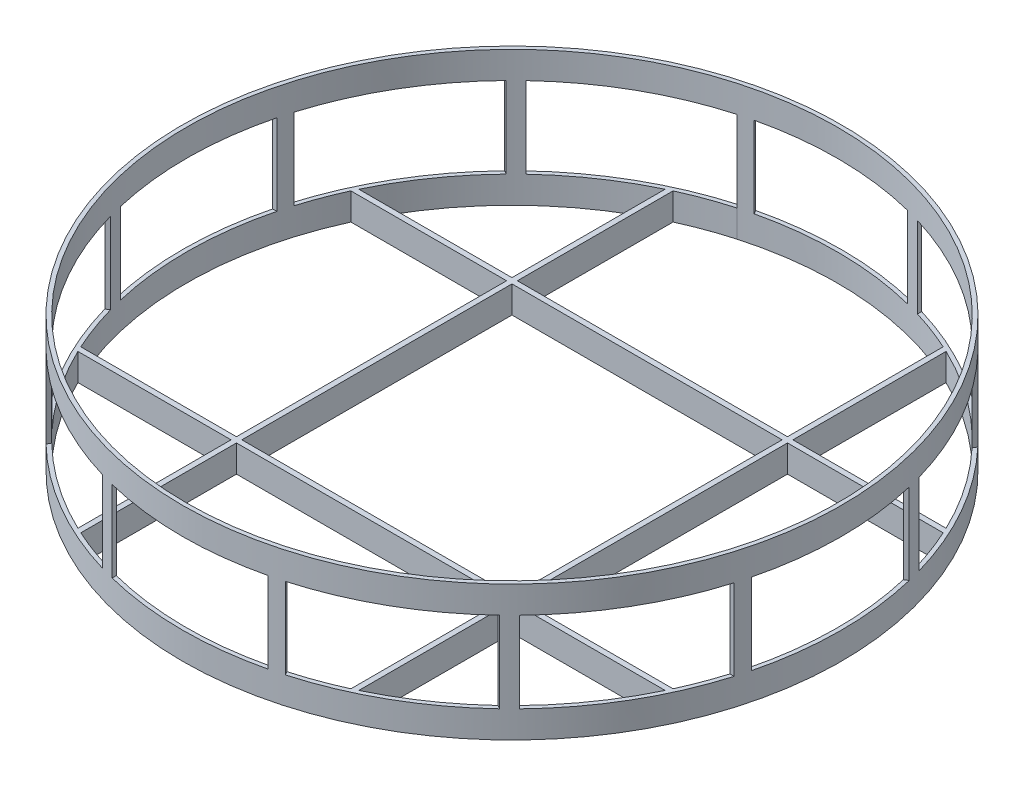
SolidWorks part; units mm, degrees
ref_plane "Front Plane" through (0, 0, 0) normal (0, 0, 1) x (1, 0, 0)
ref_plane "Top Plane" through (0, 0, 0) normal (0, 1, 0) x (1, 0, 0)
ref_plane "Right Plane" through (0, 0, 0) normal (1, 0, 0) x (0, 0, -1)
sketch "Sketch1" plane through (0, 0, 0) normal (0, 1, 0) x (1, 0, 0)
  circle A0 centre (0, 0) radius 120.5
  circle A1 centre (0, 0) radius 122
  dimension "D1" = 241
  dimension "D2" = 244
extrude "Boss-Extrude1" add sketch "Sketch1" along normal blind 10
sketch "Sketch3" plane through (0, 10, 0) normal (0, 1, 0) x (1, 0, 0)
  line L0 (34.7178, 116.9559) -> (34.7178, 115.3903)
  line L1 (29.7178, 118.3252) -> (29.7178, 116.778)
  circle A0 centre (0, 0) radius 122
  circle A1 centre (0, 0) radius 120.5
  point P8 (22.9076, 118.3025)
  point P9 (29.7178, 116.778)
  circle M1 centre (0, 0) radius 122
  circle M2 centre (0, 0) radius 120.5
  dimension "D1" = 244
  dimension "D2" = 241
  dimension "D3" = 5
extrude "Boss-Extrude2" add sketch "Sketch3" along normal blind 30 contours L1 L0 M1 M2
pattern_circular "CirPattern1" count 12 every 30 about axis through (0, 0, 0) along (0, 1, 0) of "Boss-Extrude2"
sketch "Sketch4" plane through (0, 40, 0) normal (0, 1, 0) x (1, 0, 0)
  circle A0 centre (0, 0) radius 120.5
  circle A1 centre (0, 0) radius 122
  dimension "D1" = 241
  dimension "D2" = 244
extrude "Boss-Extrude3" add sketch "Sketch4" along normal blind 10
sketch "Sketch6" plane through (0, 0, 0) normal (0, 1, 0) x (1, 0, 0)
  line L1 (-52, 109.6369) -> (-50, 109.6369)
  line L2 (-52, 109.6369) -> (-52, -109.6369)
  line L3 (-52, -109.6369) -> (-50, -109.6369)
  line L4 (-50, 109.6369) -> (-50, -109.6369)
  circle A0 centre (0, 0) radius 120.5 construction
  circle A1 centre (0, 0) radius 120.5 construction
  point P5 (-62.0899, 101.8107)
  point P8 (0, 0)
  point P10 (0, 0)
  point P13 (0, 0)
  dimension "D1" = 2
  dimension "D2" = 50
extrude "Boss-Extrude4" add sketch "Sketch6" along normal blind 10
pattern_circular "CirPattern2" count 4 every 90 about axis through (0, 0, 0) along (0, 1, 0) of "Boss-Extrude4"
